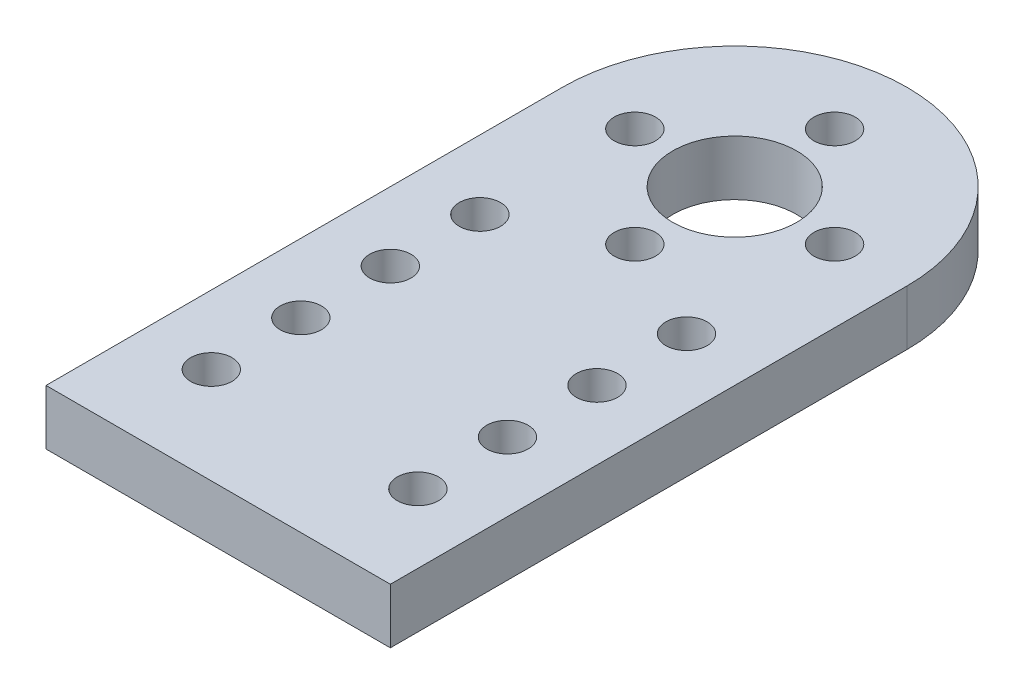
SolidWorks part; units mm, degrees
ref_plane "Спереди" through (0, 0, 0) normal (0, 0, 1) x (1, 0, 0)
ref_plane "Сверху" through (0, 0, 0) normal (0, 1, 0) x (1, 0, 0)
ref_plane "Справа" through (0, 0, 0) normal (1, 0, 0) x (0, 0, -1)
sketch "Эскиз1" plane through (0, 0, 0) normal (0, 1, 0) x (1, 0, 0)
  line L0 (-12.5, 15.8522) -> (-12.5, -21.6478)
  line L1 (-12.5, -21.6478) -> (12.5, -21.6478)
  line L2 (12.5, -21.6478) -> (12.5, 15.8522)
  line L3 (-9, -14.6478) -> (-12.5, -14.6478) construction
  line L4 (9, -14.6478) -> (12.5, -14.6478) construction
  line L5 (-6, -14.6478) -> (6, -14.6478) construction
  line L6 (7.5, -16.1478) -> (7.5, -21.6478) construction
  line L7 (7.5, -13.1478) -> (7.5, -9.6478) construction
  line L8 (-5.75, 15.8522) -> (5.75, 15.8522) construction
  arc A0 (12.5, 15.8522) -> (-12.5, 15.8522) centre (0, 15.8522) ccw
  circle A1 centre (0, 15.8522) radius 4.5
  circle A2 centre (-7.5, -14.6478) radius 1.5
  circle A3 centre (7.5, -14.6478) radius 1.5
  circle A4 centre (-7.5, -8.1478) radius 1.5
  circle A5 centre (7.5, -8.1478) radius 1.5
  circle A6 centre (-7.5, -1.6478) radius 1.5
  circle A7 centre (7.5, -1.6478) radius 1.5
  circle A8 centre (-7.5, 4.8522) radius 1.5
  circle A9 centre (7.5, 4.8522) radius 1.5
  circle A10 centre (0, 23.1022) radius 1.5
  circle A11 centre (7.25, 15.8522) radius 1.5
  circle A12 centre (0, 8.6022) radius 1.5
  circle A13 centre (-7.25, 15.8522) radius 1.5
  point P5 (0, 28.3522)
  point P6 (0, -21.6478)
  point P39 (0, 0)
  point P46 (0, 15.8522)
  dimension "D1" = 25
  dimension "D3" = 9
  dimension "D4" = 3
  dimension "D11" = 3
  dimension "D2" = 50
  dimension "D5" = 12
  dimension "D6" = 5.5
  dimension "D8" = 3.5
  dimension "D10" = 11.5
  dimension "D7" = 4
  dimension "D9" = 4
extrude "Бобышка-Вытянуть1" add sketch "Эскиз1" along normal blind 4
